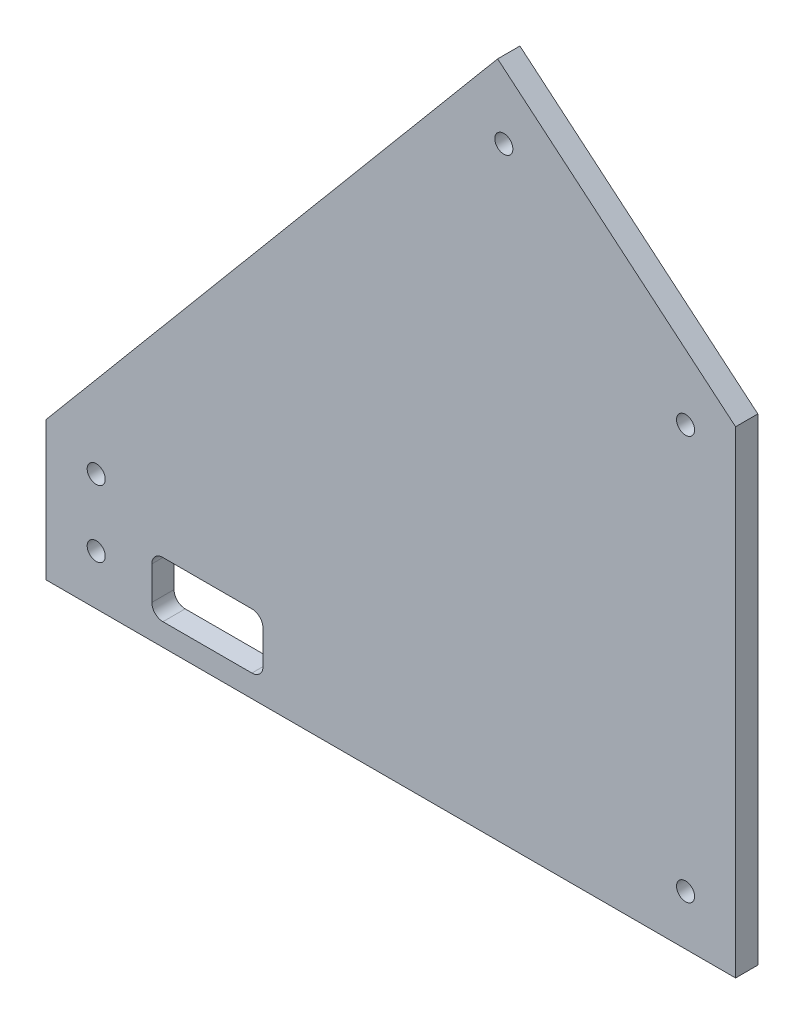
SolidWorks part; units mm, degrees
ref_plane "Front Plane" through (0, 0, 0) normal (0, 0, 1) x (1, 0, 0)
ref_plane "Top Plane" through (0, 0, 0) normal (0, 1, 0) x (1, 0, 0)
ref_plane "Right Plane" through (0, 0, 0) normal (1, 0, 0) x (0, 0, -1)
sketch "Sketch1" plane through (0, 0, 0) normal (0, 0, 1) x (1, 0, 0)
  line L5 (-38.3022, 112.1394) -> (0, 80) construction
  line L6 (0, 80) -> (0, 0) construction
  line L7 (0, 0) -> (-120, 0) construction
  line L8 (-38.3022, 112.1394) -> (-35.7311, 115.2036)
  line L9 (-35.7311, 115.2036) -> (4, 81.8652)
  line L10 (4, 81.8652) -> (4, -4)
  line L11 (4, -4) -> (-120, -4)
  line L12 (-120, -4) -> (-120, 0)
  line L13 (0, 0) -> (4, 0) construction
  line L14 (0, 80) -> (-35.198, 80) construction
  line L15 (-97.6017, 31.3568) -> (-33.3229, 107.9613) construction
  line L16 (-97.6017, 31.3568) -> (-69.258, 7.5737) construction
  line L17 (-33.3229, 107.9613) -> (-4.9793, 84.1781) construction
  line L18 (-69.258, 7.5737) -> (-4.9793, 84.1781) construction
  line L19 (-97.6017, 31.3568) -> (-4.9793, 84.1781) construction
  line L20 (-33.3229, 107.9613) -> (-69.258, 7.5737) construction
  line L21 (-51.2905, 57.7675) -> (-19.1511, 96.0697) construction
  line L22 (-38.3022, 112.1394) -> (-116.9358, 18.4275) construction
  line L23 (-120, 0) -> (-116, 0)
  line L24 (-120, 0) -> (-120, 20.9987)
  line L25 (-120, 20.9987) -> (-116, 20.9987)
  line L26 (-116, 0) -> (-116, 20.9987) construction
  line L27 (-116.9358, 18.4275) -> (-120, 20.9987) construction
  line L28 (-120, 20.9987) -> (-38.7952, 117.7747)
  line L29 (-38.7952, 117.7747) -> (-35.7311, 115.2036)
  line L30 (-106, 0) -> (-106, 31.4603) construction
  line L31 (0, 66.9459) -> (-10, 75.3369) construction
  line L32 (0, 0) -> (-10, 0)
  line L33 (0, 0) -> (0, 10)
  line L34 (0, 10) -> (-10, 10) construction
  line L35 (-10, 0) -> (-10, 10) construction
  line L36 (-10, 75.3369) -> (-10, 88.391) construction
  line L37 (-44.7301, 104.4789) -> (-37.0697, 98.0511) construction
  line L38 (-37.0697, 98.0511) -> (-30.6418, 105.7115) construction
  line L39 (-106, 12.7502) -> (-116, 12.7502) construction
  line L40 (-10, 5) -> (0, 5) construction
  line L41 (-5, 71.1414) -> (-5, 84.1955) construction
  line L42 (-5, 10) -> (-5, 0) construction
  line L43 (-10, 81.864) -> (0, 73.473) construction
  line L44 (-111, 12.7502) -> (-111, 0) construction
  line L45 (-111, 0) -> (-111, 12.7502)
  line L46 (-111, 12.7502) -> (-111, 25.5015) construction
  line L47 (-40.8999, 101.265) -> (-34.472, 108.9254) construction
  line L48 (-33.8557, 101.8813) -> (-41.5162, 108.3092) construction
  line L50 (-101, 10) -> (-81, 10)
  line L51 (-101, 10) -> (-101, 0)
  line L52 (-101, 0) -> (-81, 0)
  line L53 (-81, 10) -> (-81, 0)
  line L54 (-101, 10) -> (-81, 0) construction
  line L55 (-101, 0) -> (-81, 10) construction
  circle A0 centre (-5, 5) radius 1.625
  circle A1 centre (-111, 5) radius 1.625
  circle A2 centre (-111, 17) radius 1.625
  circle A3 centre (-37.6859, 105.0952) radius 1.625
  circle A4 centre (-5, 77.6685) radius 1.625
  point P10 (-51.2905, 57.7675)
  point P54 (-5, 5)
  point P57 (-5, 77.6685)
  point P64 (-37.6859, 105.0952)
  point P65 (-91, 5)
  dimension "D10" = 3.25
  dimension "D1" = 4
  dimension "D2" = 120
  dimension "D3" = 80
  dimension "D4" = 50
  dimension "D5" = 40
  dimension "D6" = 37
  dimension "D7" = 100
  dimension "D8" = 10
  dimension "D9" = 12
  dimension "D11" = 20
  dimension "D12" = 10
  dimension "D13" = 20
extrude "Boss-Extrude1" add sketch "Sketch1" along normal blind 4
fillet "Fillet1" radius 2 4 edges at (-81, 10, 2) (-81, 0, 2) (-101, 0, 2) (-101, 10, 2)
